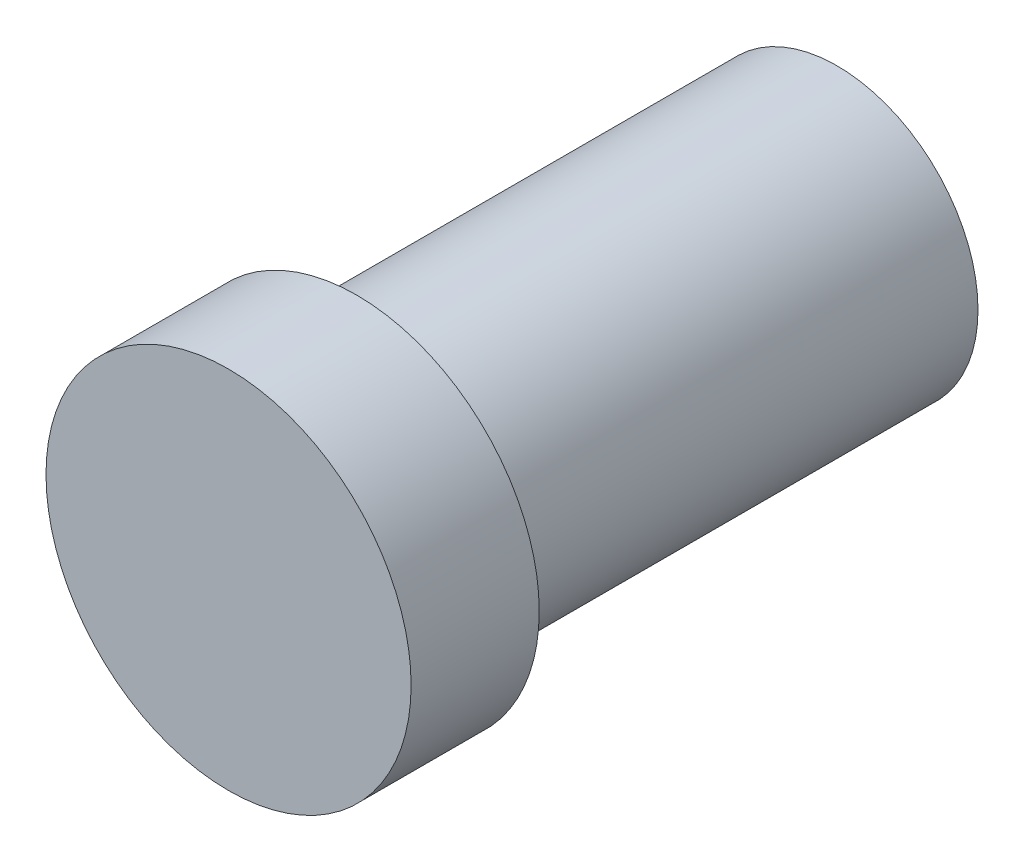
SolidWorks part; units mm, degrees
ref_plane "Front Plane" through (0, 0, 0) normal (0, 0, 1) x (1, 0, 0)
ref_plane "Top Plane" through (0, 0, 0) normal (0, 1, 0) x (1, 0, 0)
ref_plane "Right Plane" through (0, 0, 0) normal (1, 0, 0) x (0, 0, -1)
sketch "Sketch1" plane through (0, 0, 0) normal (0, 0, 1) x (1, 0, 0)
  circle A0 centre (0, 0) radius 22
  dimension "D1" = 44
extrude "Boss-Extrude1" add sketch "Sketch1" against normal blind 75
sketch "Sketch2" plane through (0, 0, 0) normal (0, 0, 1) x (1, 0, 0)
  circle A0 centre (0, 0) radius 28.5
  dimension "D1" = 57
extrude "Boss-Extrude2" add sketch "Sketch2" along normal blind 20
fillet "Fillet1" radius 2 1 edges at (22, 0, 0)
